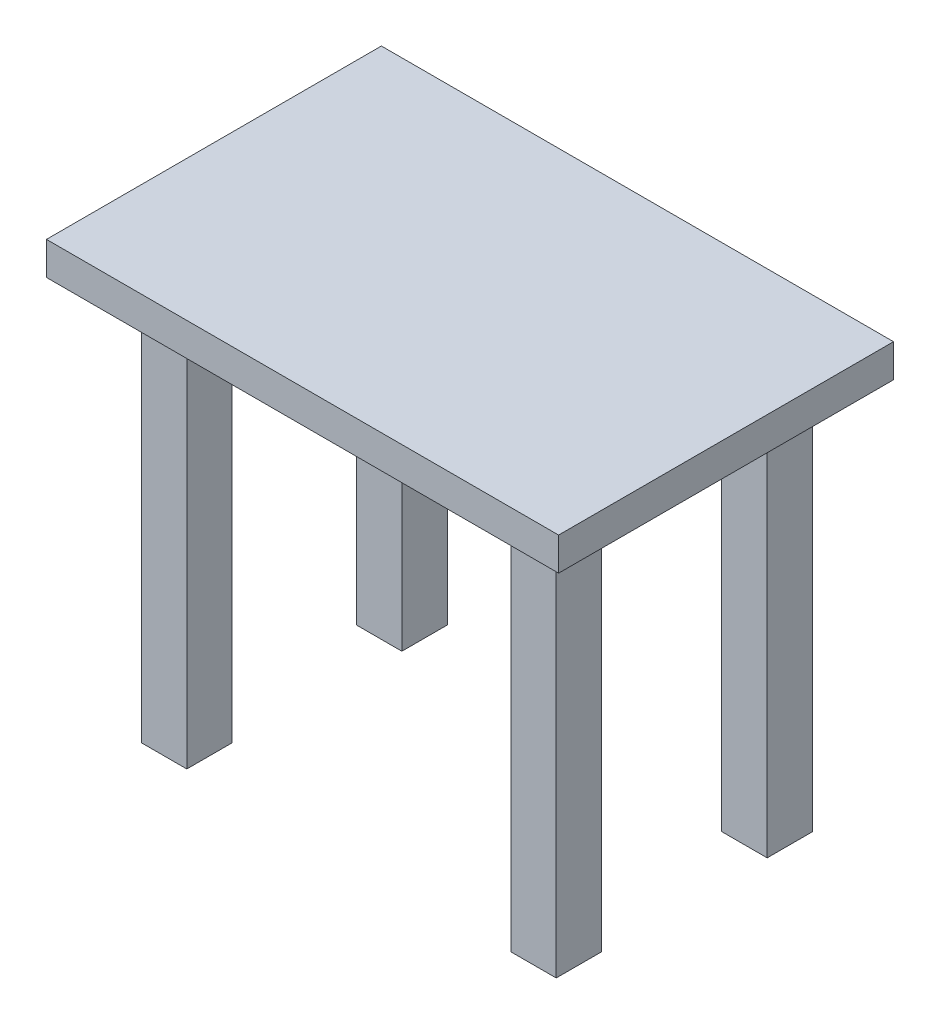
SolidWorks part; units mm, degrees
material "AISI 316 Stainless Steel Sheet (SS)"
ref_plane "Front Plane" through (0, 0, 0) normal (0, 0, 1) x (1, 0, 0)
ref_plane "Top Plane" through (0, 0, 0) normal (0, 1, 0) x (1, 0, 0)
ref_plane "Right Plane" through (0, 0, 0) normal (1, 0, 0) x (0, 0, -1)
sketch "Sketch1" plane through (0, 0, 0) normal (0, 1, 0) x (1, 0, 0)
  line L1 (77.605, -50.7505) -> (-77.605, -50.7505)
  line L2 (77.605, -50.7505) -> (77.605, 50.7505)
  line L3 (77.605, 50.7505) -> (-77.605, 50.7505)
  line L4 (-77.605, -50.7505) -> (-77.605, 50.7505)
  line L5 (77.605, -50.7505) -> (-77.605, 50.7505) construction
  line L6 (77.605, 50.7505) -> (-77.605, -50.7505) construction
  point P0 (0, 0)
extrude "Boss-Extrude1" add sketch "Sketch1" against normal blind 10
sketch "Sketch2" plane through (0, 0, 0) normal (0, 1, 0) x (1, 0, 0)
  line L0 (63.9312, 26.1279) -> (50.1651, 26.1279)
  line L1 (-45.653, 25.0038) -> (-59.4191, 25.0038)
  line L2 (-45.653, 25.0038) -> (-45.653, 38.7699)
  line L3 (-45.653, 38.7699) -> (-59.4191, 38.7699)
  line L4 (-59.4191, 25.0038) -> (-59.4191, 38.7699)
  line L5 (-45.653, 25.0038) -> (-59.4191, 38.7699) construction
  line L6 (-45.653, 38.7699) -> (-59.4191, 25.0038) construction
  line L7 (63.9312, 26.1279) -> (63.9312, 39.894)
  line L8 (63.9312, 39.894) -> (50.1651, 39.894)
  line L9 (50.1651, 26.1279) -> (50.1651, 39.894)
  line L10 (-47.3386, -38.489) -> (-61.1048, -38.489)
  line L11 (-47.3386, -38.489) -> (-47.3386, -24.7228)
  line L12 (-47.3386, -24.7228) -> (-61.1048, -24.7228)
  line L13 (-61.1048, -38.489) -> (-61.1048, -24.7228)
  line L14 (63.4928, -37.3652) -> (49.7266, -37.3652)
  line L15 (63.4928, -37.3652) -> (63.4928, -23.5991)
  line L16 (63.4928, -23.5991) -> (49.7266, -23.5991)
  line L17 (49.7266, -37.3652) -> (49.7266, -23.5991)
  point P0 (-52.5361, 31.8869)
extrude "Boss-Extrude2" add sketch "Sketch2" against normal blind 130
